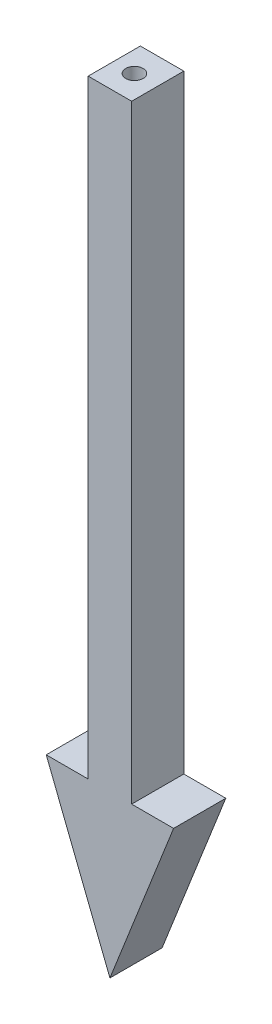
SolidWorks part; units mm, degrees
ref_plane "Front Plane" through (0, 0, 0) normal (0, 0, 1) x (1, 0, 0)
ref_plane "Top Plane" through (0, 0, 0) normal (0, 1, 0) x (1, 0, 0)
ref_plane "Right Plane" through (0, 0, 0) normal (1, 0, 0) x (0, 0, -1)
sketch "Sketch1" plane through (0, 0, 0) normal (0, 0, 1) x (1, 0, 0)
  line L0 (-9.5412, 105.4982) -> (-9.5412, 95.4982)
  line L1 (0.4588, 105.4982) -> (0.4588, 95.4982)
  line L7 (-9.5412, 105.4982) -> (0.4588, 105.4982)
  line L8 (0.4588, 95.4982) -> (0.4588, -34.5018)
  line L9 (0.4588, -34.5018) -> (10.1106, -34.5018)
  line L10 (-4.5412, -71.6321) -> (10.1106, -34.5018)
  line L11 (-19.1929, -34.5018) -> (-4.5412, -71.6321)
  line L12 (-19.1929, -34.5018) -> (-9.5412, -34.5018)
  line L13 (-9.5412, 95.4982) -> (-9.5412, -34.5018)
extrude "Boss-Extrude1" add sketch "Sketch1" along normal blind 12
sketch "Sketch2" plane through (0, 105.4982, 0) normal (0, 1, 0) x (1, 0, 0)
  circle A0 centre (-4.7459, -6.1535) radius 2
extrude "Cut-Extrude1" cut sketch "Sketch2" against normal blind 10
